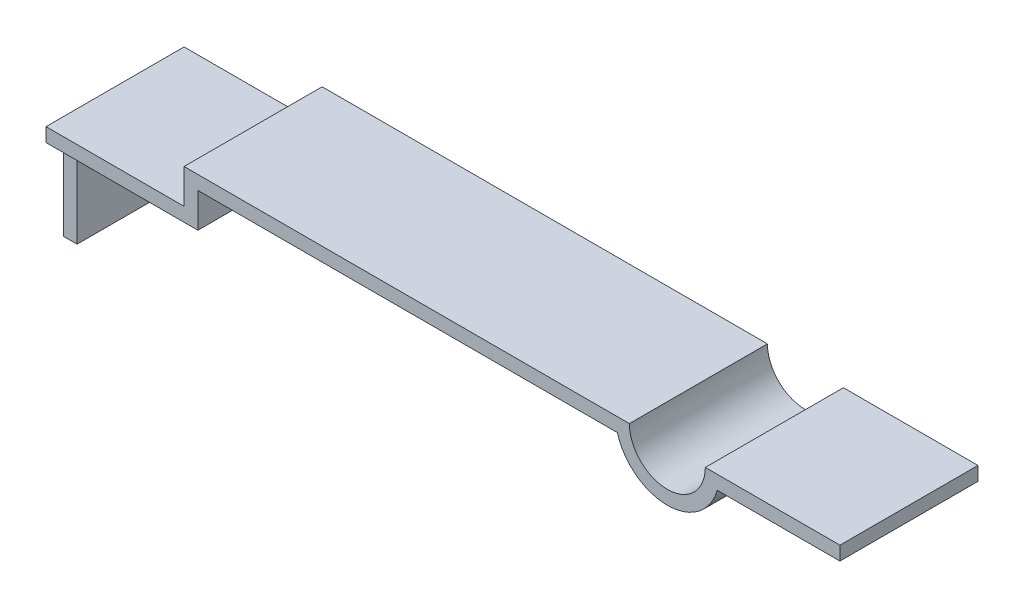
SolidWorks part; units mm, degrees
ref_plane "Front" through (0, 0, 0) normal (0, 0, 1) x (1, 0, 0)
ref_plane "Top" through (0, 0, 0) normal (0, 1, 0) x (1, 0, 0)
ref_plane "Right" through (0, 0, 0) normal (1, 0, 0) x (0, 0, -1)
sketch "草图1" plane through (0, 0, 0) normal (0, 0, 1) x (1, 0, 0)
  line L0 (0, 0) -> (0, 0.5)
  line L1 (0, 0.5) -> (6.45, 0.5)
  line L2 (0, 0) -> (-2, 0)
  line L3 (-2, 0) -> (-2, -1.5)
  line L4 (7.55, 0.5) -> (9.5, 0.5)
  line L5 (7.7228, 0.3) -> (9.5, 0.3)
  line L6 (0.2, 0.3) -> (6.2772, 0.3)
  line L7 (0.2, -0.2) -> (0.2, 0.3)
  line L8 (0.2, -0.2) -> (-1.8, -0.2)
  line L9 (-1.8, -0.2) -> (-1.8, -1.5)
  line L10 (-2, -1.5) -> (-1.8, -1.5)
  line L11 (9.5, 0.5) -> (9.5, 0.3)
  arc A0 (6.45, 0.5) -> (7.55, 0.5) centre (7, 0.5) ccw
  arc A1 (6.2772, 0.3) -> (7.7228, 0.3) centre (7, 0.5) ccw
  dimension "D4" = 90
  dimension "D1" = 1.5
  dimension "D5" = 1.1
  dimension "D2" = 2
  dimension "D3" = 0.5
  dimension "D6" = 9.5
  dimension "D7" = 7
  dimension "D8" = 0.2
extrude "凸台-拉伸1" add sketch "草图1" along normal blind 2
sketch "草图3" plane through (-1.8, 0, 0) normal (1, 0, 0) x (0, 0, -1)
  line L1 (-2, -0.2) -> (0, -0.2) construction
  line L2 (-2, -1.5) -> (-1.75, -1.5)
  line L3 (-2, -1.5) -> (-2, -0.2)
  line L4 (-2, -0.2) -> (-1.75, -0.2)
  line L5 (-1.75, -1.5) -> (-1.75, -0.2)
  line L7 (0, -1.5) -> (-0.25, -1.5)
  line L8 (0, -1.5) -> (0, -0.2)
  line L9 (0, -0.2) -> (-0.25, -0.2)
  line L10 (-0.25, -1.5) -> (-0.25, -0.2)
  dimension "D1" = 0.25
  dimension "D2" = 0.25
extrude "切除-拉伸2" cut sketch "草图3" against normal through all
